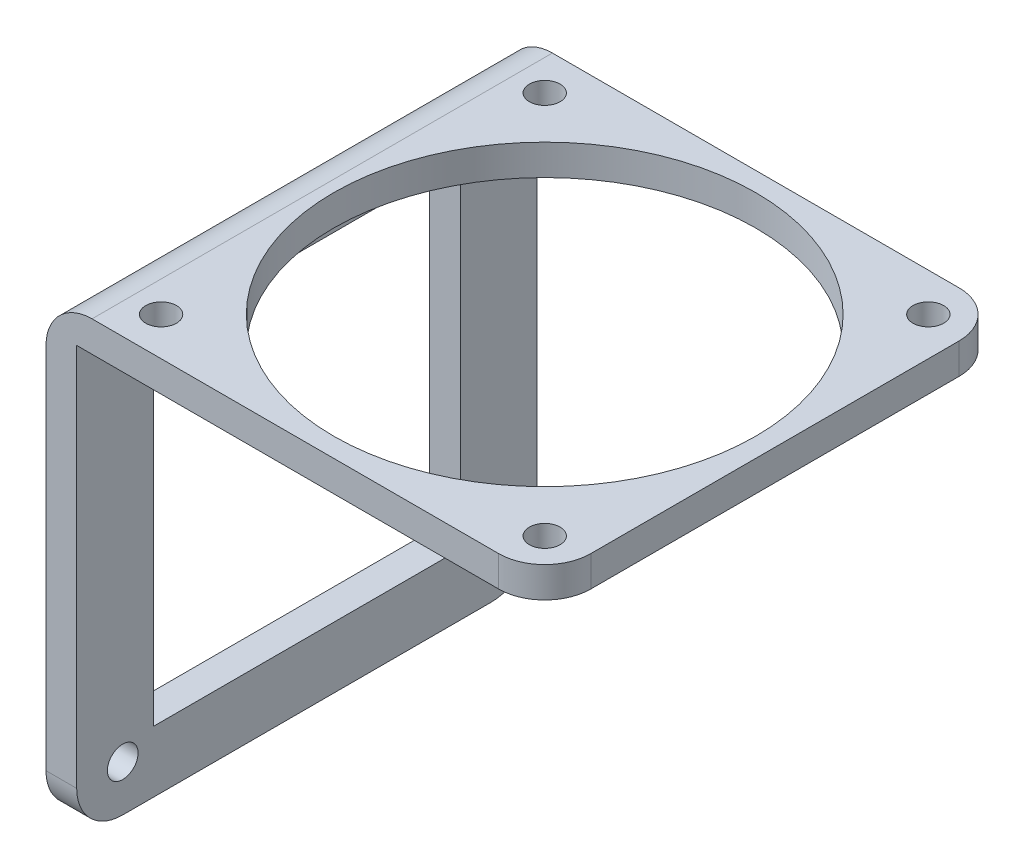
SolidWorks part; units mm, degrees
ref_plane "Front" through (0, 0, 0) normal (0, 0, 1) x (1, 0, 0)
ref_plane "Top" through (0, 0, 0) normal (0, 1, 0) x (1, 0, 0)
ref_plane "Right" through (0, 0, 0) normal (1, 0, 0) x (0, 0, -1)
sketch "Esboço1" plane through (0, 0, 0) normal (0, 0, 1) x (1, 0, 0)
  line L8 (0, 0) -> (4, 0)
  line L9 (4, 0) -> (4, 56)
  line L10 (4, 56) -> (65, 56)
  line L11 (65, 56) -> (65, 60)
  line L12 (65, 60) -> (0, 60)
  line L13 (0, 60) -> (0, 0)
  dimension "D1" = 4
  dimension "D2" = 90
  dimension "D3" = 65
  dimension "D4" = 60
extrude "Ressalto-extrusão1" add sketch "Esboço1" along normal blind 60
sketch "Esboço2" plane through (0, 0, 0) normal (-1, 0, 0) x (0, 0, 1)
  line L1 (10, 8) -> (50, 8)
  line L2 (10, 8) -> (10, 52)
  line L3 (10, 52) -> (50, 52)
  line L4 (50, 8) -> (50, 52)
  line L5 (10, 8) -> (50, 52) construction
  line L6 (10, 52) -> (50, 8) construction
  line L7 (0, 60) -> (0, 0) construction
  line L8 (60, 60) -> (60, 0) construction
  line L9 (60, 0) -> (0, 0) construction
  line L10 (60, 60) -> (0, 60) construction
  point P4 (30, 30)
  point P13 (0, 0)
  dimension "D1" = 10
  dimension "D2" = 10
  dimension "D3" = 8
  dimension "D4" = 8
extrude "Corte-extrusão1" cut sketch "Esboço2" against normal through all
sketch "Esboço4" plane through (0, 60, 0) normal (0, 1, 0) x (0, 0, 1)
  line L0 (60, 65) -> (0, 65) construction
  line L1 (5, 60) -> (55, 60) construction
  line L2 (5, 60) -> (5, 10) construction
  line L3 (5, 10) -> (55, 10) construction
  line L4 (55, 60) -> (55, 10) construction
  line L5 (5, 60) -> (55, 10) construction
  line L6 (5, 10) -> (55, 60) construction
  circle A0 centre (5, 60) radius 2
  circle A1 centre (55, 60) radius 2
  circle A2 centre (5, 10) radius 2
  circle A3 centre (55, 10) radius 2
  point P2 (30, 60)
  point P13 (30, 35)
  point P14 (30, 65)
  dimension "D1" = 4
  dimension "D2" = 50
  dimension "D3" = 5
extrude "Corte-extrusão3" cut sketch "Esboço4" against normal up to next
sketch "Esboço5" plane through (0, 56, 0) normal (0, -1, 0) x (0, 0, -1)
  line L12 (-5, 60) -> (-55, 60) construction
  line L14 (-5, 60) -> (-5, 10) construction
  line L15 (-5, 10) -> (-55, 10) construction
  line L16 (-55, 60) -> (-55, 10) construction
  line L17 (-5, 60) -> (-55, 10) construction
  line L18 (-5, 10) -> (-55, 60) construction
  circle A0 centre (-30, 35) radius 27.5
  point P2 (-30, 35)
  point P14 (-30, 35)
  dimension "D1" = 55
extrude "Corte-extrusão4" cut sketch "Esboço5" against normal through all
sketch "Esboço6" plane through (0, 0, 0) normal (-1, 0, 0) x (0, 0, 1)
  line L0 (60, 0) -> (0, 0) construction
  line L1 (0, 60) -> (0, 0) construction
  line L2 (60, 60) -> (60, 0) construction
  circle A0 centre (6, 6) radius 2
  circle A1 centre (54, 6) radius 2
  point P4 (0, 0)
  dimension "D1" = 4
  dimension "D2" = 6
  dimension "D3" = 6
  dimension "D4" = 6
extrude "Corte-extrusão5" cut sketch "Esboço6" against normal blind 10
fillet "Filete2" radius 6 5 edges at (65, 58, 60) (65, 58, 0) (0, 60, 30) (2, 0, 60) (2, 0, 0)
equation "\"D2@Esboço2\"=\"D1@Esboço2\""
equation "\"D4@Esboço2\"=\"D3@Esboço2\""
equation "\"D3@Esboço4\"=(60-\"D2@Esboço4\")/2"
